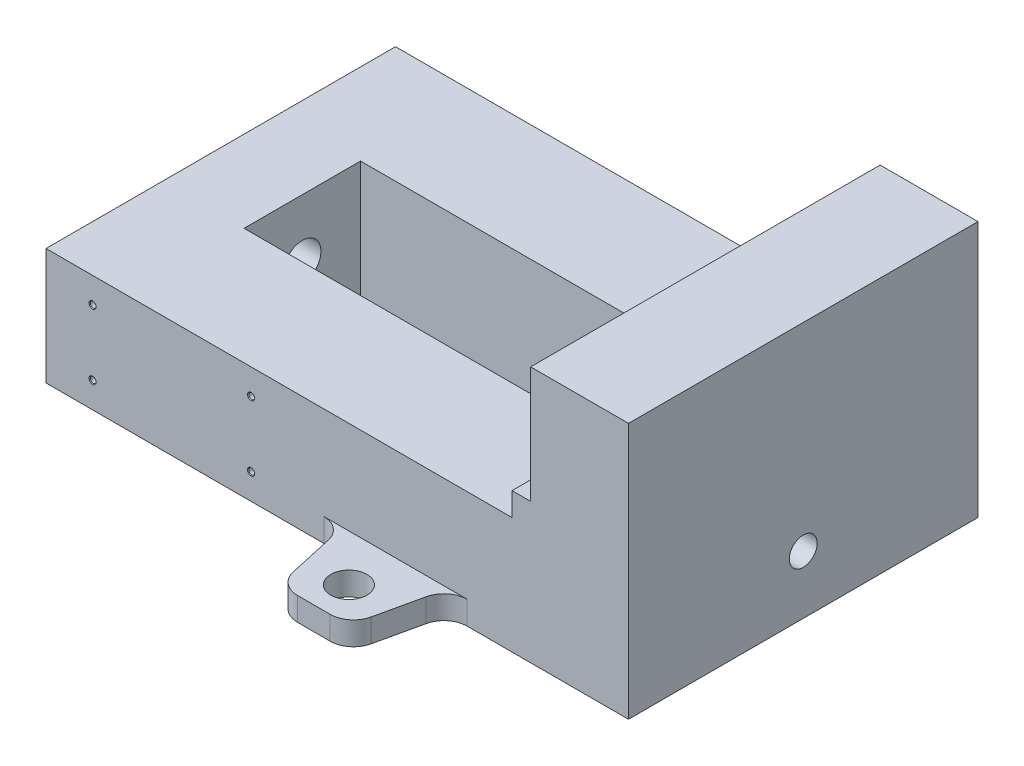
SolidWorks part; units mm, degrees
ref_plane "Front Plane" through (0, 0, 0) normal (0, 0, 1) x (1, 0, 0)
ref_plane "Top Plane" through (0, 0, 0) normal (0, 1, 0) x (1, 0, 0)
ref_plane "Right Plane" through (0, 0, 0) normal (1, 0, 0) x (0, 0, -1)
sketch "Sketch1" plane through (0, 0, 0) normal (0, 0, 1) x (1, 0, 0)
  line L0 (0, 0) -> (250, 0)
  line L1 (250, 0) -> (250, 110)
  line L2 (250, 110) -> (208, 110)
  line L3 (208, 110) -> (208, 60)
  line L4 (208, 60) -> (200, 60)
  line L5 (200, 60) -> (200, 50)
  line L6 (200, 50) -> (0, 50)
  line L7 (0, 50) -> (0, 0)
  point P9 (0, 0)
  point P10 (0, 0)
  point P11 (0, 0)
  point P12 (0, 0)
  dimension "D1" = 250
  dimension "D2" = 110
  dimension "D3" = 50
  dimension "D4" = 8
  dimension "D5" = 50
  dimension "D6" = 60
extrude "Boss-Extrude2" add sketch "Sketch1" along normal mid plane 150
sketch "Sketch3" plane through (0, 0, 0) normal (-1, 0, 0) x (0, 0, 1)
  line L3 (75, 50) -> (-75, 50) construction
  line L4 (25, 0) -> (-25, 0)
  line L5 (75, 0) -> (-75, 0) construction
  line L6 (-25, 0) -> (-25, 50)
  line L7 (-25, 50) -> (25, 50)
  line L8 (0, 0) -> (0, 50) construction
  line L9 (25, 0) -> (25, 50)
  dimension "D1" = 25
extrude "Cut-Extrude1" cut sketch "Sketch3" against normal up to surface (165 mm away) from offset 35 up to face at (200, 55, 0) offset against normal yes
sketch "Sketch4" plane through (0, 0, 0) normal (-1, 0, 0) x (0, 0, 1)
  line L0 (75, 0) -> (-75, 0) construction
  circle A0 centre (0, 25) radius 14
  point P6 (0, 0)
  point P7 (0, 0)
  point P9 (0, 0)
  dimension "D1" = 28
  dimension "D2" = 25
extrude "Boss-Extrude3" add sketch "Sketch4" along normal blind 5
sketch "Sketch5" plane through (250, 0, 0) normal (1, 0, 0) x (0, 0, -1)
  line L0 (-75, 0) -> (75, 0) construction
  circle A0 centre (0, 25) radius 6
  point P5 (0, 0)
  dimension "D1" = 12
  dimension "D2" = 25
extrude "Cut-Extrude2" cut sketch "Sketch5" against normal up to next and the other way through all
sketch "Sketch9" plane through (-5, 0, 0) normal (-1, 0, 0) x (0, 0, 1)
  circle A0 centre (0, 25) radius 8
  circle A1 centre (0, 25) radius 14 construction
  point P3 (0, 0)
  dimension "D1" = 16
extrude "Cut-Extrude4" cut sketch "Sketch9" against normal up to next
fillet "Fillet2" radius 3 1 edges at (0, 11, 0)
sketch "Sketch10" plane through (208, 0, 0) normal (-1, 0, 0) x (0, 0, 1)
  line L0 (75, 60) -> (-75, 60) construction
  line L2 (75, 110) -> (75, 60) construction
  point P0 (-45, 85)
  point P1 (45, 85)
  point P6 (-149.8875, 104.136)
  dimension "D1" = 90
  dimension "D2" = 25
  dimension "D3" = 30
hole_wizard "M6x1.0 Tapped Hole2" positions "3DSketch2" profile "Sketch12" tap size "M6x1.0" standard "ANSI Metric"
sketch3d "3DSketch2"
  point P0 (208, 85, -45)
  point P3 (208, 85, 45)
sketch "Sketch12" plane through (208, 85, -45) normal (0, 1, 0) x (0, 0, 1)
  line L0 (0, 0) -> (0, 18.6)
  line L1 (0, 18.6) -> (2.5, 17.0978)
  line L2 (2.5, 17.0978) -> (2.5, 0.525)
  line L3 (2.5, 0.525) -> (3.025, 0)
  line L5 (3.025, 0) -> (0, 0)
  line L6 (-2.5, 0.525) -> (-3.025, 0) construction
  line L10 (0, 18.6) -> (-2.5, 17.0978) construction
  line L11 (0, -6.35) -> (0, 107.95) construction
  dimension "Tap Drill Dia." = 5
  dimension "Tap Drill Depth" = 18.6
  dimension "Near C'Sink Dia." = 6.05
  dimension "Near C'Sink Angle" = 90
  dimension "Drill Angle" = 118
cosmetic thread "Hole Thread3" parameters "D1"=12, "D2"=6
cosmetic thread "Hole Thread4" parameters "D1"=12, "D2"=6
sketch "Sketch13" plane through (0, 0, 75) normal (0, 0, 1) x (1, 0, 0)
  line L0 (0, 50) -> (0, 0) construction
  line L1 (200, 50) -> (0, 50) construction
  point P0 (20, 39)
  point P1 (88, 39)
  point P2 (88, 11)
  point P3 (20, 11)
  point P4 (0, 0)
  point P5 (0, 0)
  point P6 (0, 0)
  point P9 (0, 0)
  point P10 (0, 0)
  point P11 (0, 0)
  dimension "D1" = 68
  dimension "D2" = 20
  dimension "D3" = 28
  dimension "D4" = 11
hole_wizard "M3x0.5 Tapped Hole1" positions "3DSketch3" profile "Sketch14" tap size "M3x0.5" standard "ANSI Metric"
sketch3d "3DSketch3"
  point P0 (20, 39, 75)
  point P3 (88, 39, 75)
  point P6 (88, 11, 75)
  point P9 (20, 11, 75)
sketch "Sketch14" plane through (20, 39, 75) normal (1, 0, 0) x (0, -1, 0)
  line L0 (0, 0) -> (0, 9.5)
  line L1 (0, 9.5) -> (1.25, 8.7489)
  line L2 (1.25, 8.7489) -> (1.25, 0.275)
  line L3 (1.25, 0.275) -> (1.525, 0)
  line L5 (1.525, 0) -> (0, 0)
  line L6 (-1.25, 0.275) -> (-1.525, 0) construction
  line L10 (0, 9.5) -> (-1.25, 8.7489) construction
  line L11 (0, -6.35) -> (0, 107.95) construction
  dimension "Tap Drill Dia." = 2.5
  dimension "Tap Drill Depth" = 9.5
  dimension "Near C'Sink Dia." = 3.05
  dimension "Near C'Sink Angle" = 90
  dimension "Drill Angle" = 118
cosmetic thread "Hole Thread5" parameters "D1"=6, "D2"=3
cosmetic thread "Hole Thread6" parameters "D1"=6, "D2"=3
cosmetic thread "Hole Thread7" parameters "D1"=6, "D2"=3
cosmetic thread "Hole Thread8" parameters "D1"=6, "D2"=3
sketch "Sketch15" plane through (0, 0, 0) normal (0, 1, 0) x (1, 0, 0)
  line L0 (127.2407, -75) -> (172.7593, -75)
  line L1 (200, -75) -> (0, -75) construction
  line L2 (135, -110) -> (165, -110)
  line L3 (135, -110) -> (127.2407, -75)
  line L4 (208, -75) -> (200, -75) construction
  line L5 (165, -110) -> (172.7593, -75)
  point P0 (150, -110)
  point P9 (0, 0)
  dimension "D1" = 30
  dimension "D" = 35
  dimension "D3" = 102.5
extrude "Boss-Extrude4" add sketch "Sketch15" along normal blind 10 contours L3 L0 L5 L2
sketch "Sketch17" plane through (0, 10, 0) normal (0, 1, 0) x (1, 0, 0)
  line L0 (127.2407, -75) -> (172.7593, -75) construction
  circle A0 centre (150, -95) radius 7.75
  dimension "D1" = 15.5
  dimension "D2" = 20
  dimension "D3" = 100
extrude "Cut-Extrude5" cut sketch "Sketch17" against normal through all both and the other way through all
fillet "Fillet3" radius 10 4 edges at (172.7593, 5, 75) (165, 5, 110) (135, 5, 110) (127.2407, 5, 75)
mirror "Mirror3" about plane through (0, 0, 0) normal (0, 0, 1) of "Boss-Extrude4", "Cut-Extrude5"
fillet "Fillet4" radius 10 4 edges at (172.7593, 5, -75) (127.2407, 5, -75) (135, 5, -110) (165, 5, -110)
